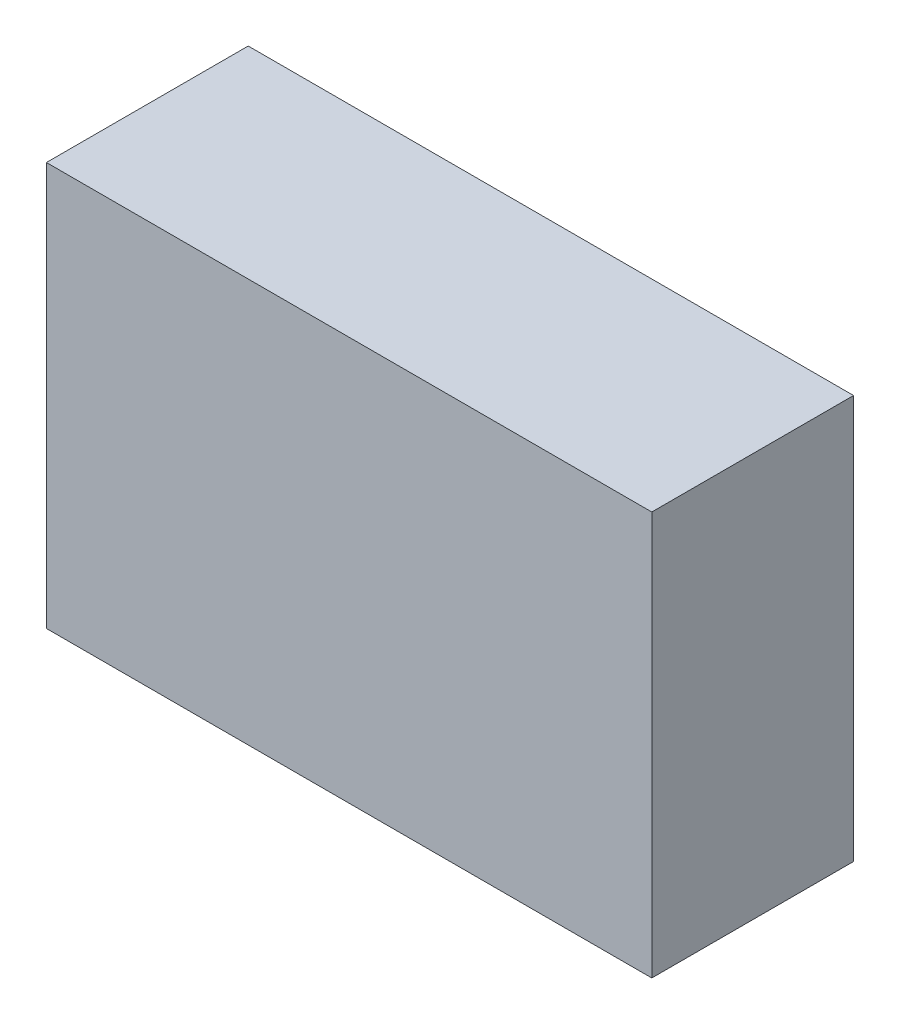
SolidWorks part; units mm, degrees
ref_plane "Alzado" through (0, 0, 0) normal (0, 0, 1) x (1, 0, 0)
ref_plane "Planta" through (0, 0, 0) normal (0, 1, 0) x (1, 0, 0)
ref_plane "Vista lateral" through (0, 0, 0) normal (1, 0, 0) x (0, 0, -1)
sketch "Croquis1" plane through (0, 0, 0) normal (0, 1, 0) x (1, 0, 0)
  line L1 (-22.5, -7.5) -> (22.5, -7.5)
  line L2 (-22.5, -7.5) -> (-22.5, 7.5)
  line L3 (-22.5, 7.5) -> (22.5, 7.5)
  line L4 (22.5, -7.5) -> (22.5, 7.5)
  line L5 (-22.5, -7.5) -> (22.5, 7.5) construction
  line L6 (-22.5, 7.5) -> (22.5, -7.5) construction
  point P0 (0, 0)
  dimension "D1" = 45
  dimension "D2" = 15
extrude "Saliente-Extruir1" add sketch "Croquis1" along normal blind 30
